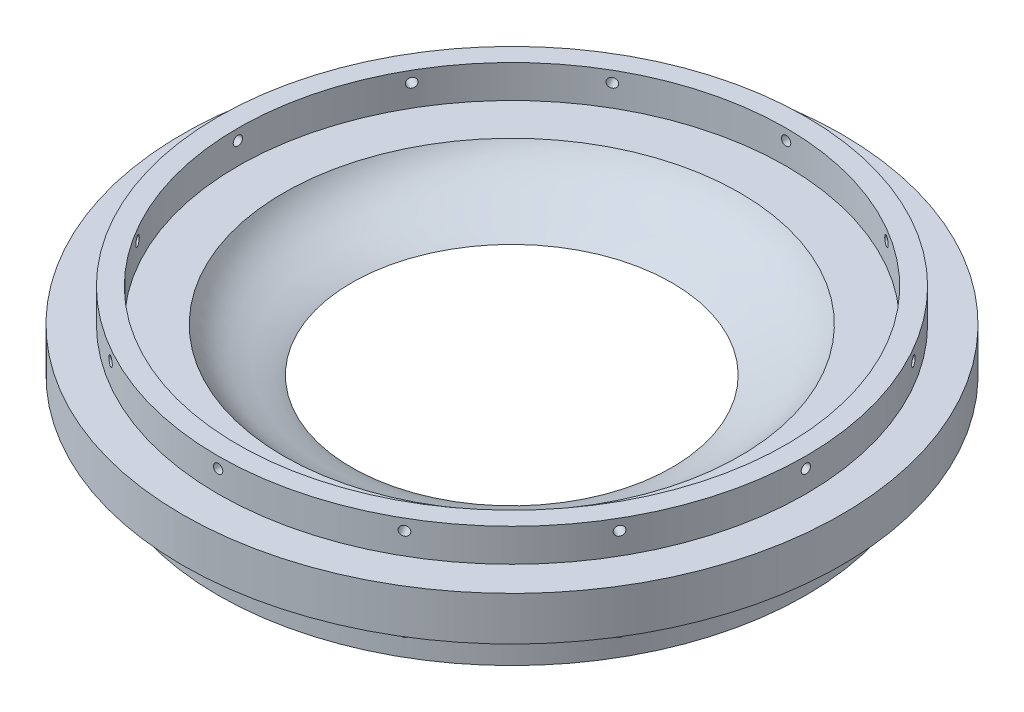
SolidWorks part; units mm, degrees
material "6061-T6 (SS)"
ref_plane "Front Plane" through (0, 0, 0) normal (0, 0, 1) x (1, 0, 0)
ref_plane "Top Plane" through (0, 0, 0) normal (0, 1, 0) x (1, 0, 0)
ref_plane "Right Plane" through (0, 0, 0) normal (1, 0, 0) x (0, 0, -1)
sketch "Sketch1" plane through (0, 0, 0) normal (0, 1, 0) x (1, 0, 0)
  line L5 (0, 0) -> (127.635, 0)
  line L6 (0, 0) -> (0, 127.635)
  line L7 (0, 127.635) -> (127.635, 127.635)
  line L8 (127.635, 0) -> (127.635, 127.635)
  dimension "D1" = 127.635
  dimension "D2" = 127.635
extrude "Boss-Extrude1" add sketch "Sketch1" along normal blind 12.7 contours L5 L8 L7 L6
sketch "Sketch12" plane through (0, 0, 0) normal (0, -1, 0) x (1, 0, 0)
  line L0 (63.8175, 0) -> (63.8175, -127.635) construction
  line L1 (0, 0) -> (127.635, 0) construction
  line L2 (0, -127.635) -> (127.635, -127.635) construction
  line L3 (0, -63.8175) -> (127.635, -63.8175) construction
  line L4 (0, 0) -> (0, -127.635) construction
  line L5 (127.635, 0) -> (127.635, -127.635) construction
  circle A0 centre (63.8175, -63.8175) radius 95.4151
  dimension "D1" = 190.8302
extrude "Boss-Extrude2" add sketch "Sketch12" against normal up to surface (12.7 mm away) contours A0 up to face at (63.8175, 12.7, -63.8175)
sketch "Sketch5" plane through (0, 12.7, 0) normal (0, 1, 0) x (1, 0, 0)
  circle A0 centre (63.8175, 63.8175) radius 46.355
  circle A3 centre (63.8175, 63.8175) radius 95.4151 construction
  dimension "D1" = 92.71
extrude "Cut-Extrude1" cut sketch "Sketch5" against normal blind 9.525
sketch "Sketch14" plane through (0, 12.7, 0) normal (0, -1, 0) x (1, 0, 0)
  line L0 (63.8175, -63.8175) -> (147.6375, -63.8175) construction
  line L1 (0, -19.2087) -> (0, 19.2087) construction
  line L2 (147.6375, -63.8175) -> (152.7175, -63.8175)
  line L3 (136.3808, -105.7742) -> (140.8401, -108.2104)
  circle A0 centre (63.8175, -63.8175) radius 46.355 construction
  arc A2 (147.6375, -63.8175) -> (136.3808, -105.7742) centre (63.8175, -63.8175) cw
  arc A3 (152.7175, -63.8175) -> (140.8401, -108.2104) centre (63.8175, -63.8175) cw
  point P0 (63.8175, -63.8175)
  dimension "D1" = 83.82
  dimension "D2" = 88.9
  dimension "D3" = 46.482
  dimension "D4" = 43.942
ref_plane "Support mirror reference plane" through (0, 4.7625, 0) normal (0, 1, 0) x (1, 0, 0)
sketch "Sketch25" plane through (0, 12.7, 0) normal (0, -1, 0) x (1, 0, 0)
  line L0 (63.8175, -63.8175) -> (123.0872, -4.5478) construction
  line L2 (123.0872, -4.5478) -> (126.6793, -0.9557)
  line L3 (144.7953, -42.1754) -> (149.6712, -40.7448)
  line L5 (63.8175, -63.8175) -> (147.6375, -63.8175) construction
  arc A2 (123.0872, -4.5478) -> (144.7953, -42.1754) centre (63.8175, -63.8175) cw
  arc A3 (126.6793, -0.9557) -> (149.6712, -40.7448) centre (63.8175, -63.8175) cw
  point P0 (63.8175, -63.8175)
  dimension "D1" = 83.82
  dimension "D2" = 88.9
  dimension "D3" = 46.482
  dimension "D4" = 43.942
  dimension "D5" = 45
sketch "Sketch30" plane through (0, 0, 0) normal (0, -1, 0) x (1, 0, 0)
  circle A0 centre (63.8175, -63.8175) radius 85.09
  circle A1 centre (63.8175, -63.8175) radius 79.375
  dimension "D1" = 170.18
  dimension "D2" = 158.75
extrude "Boss-Extrude3" add sketch "Sketch30" along normal blind 12.7
mirror "Mirror1" about plane through (0, 4.7625, 0) normal (0, 1, 0) of "Boss-Extrude3"
sketch "Sketch31" plane through (0, 0, 0) normal (0, -1, 0) x (-1, 0, 0)
  line L0 (-63.8175, -52.481) -> (-63.8175, 177.7216) construction
ref_plane "Plane1" through (0, 0, -148.9075) normal (0, 0, -1) x (-1, 0, 0)
ref_plane "Plane2" through (63.8175, 0, 0) normal (-1, 0, 0) x (0, 0, -1)
sketch "Sketch32" plane through (0, 0, -148.9075) normal (0, 0, -1) x (-1, 0, 0)
  line L4 (-63.8175, -87.3125) -> (-63.8175, 87.3125) construction
  line L5 (-148.9075, 0) -> (21.2725, 0) construction
  line L6 (21.2725, 12.7) -> (-148.9075, 12.7) construction
  circle A0 centre (-63.8175, -6.35) radius 1.3526
  circle A1 centre (-63.8175, 19.05) radius 1.3525
  dimension "D1" = 2.7051
  dimension "D2" = 2.7051
  dimension "D3" = 6.35
  dimension "D4" = 6.35
extrude "Cut-Extrude4" cut sketch "Sketch32" against normal blind 15.24
pattern_circular "CirPattern2" count 12 over 360 about axis through (63.8175, -12.7, -63.8175) along (0, 1, 0) of "Cut-Extrude4"
ref_plane "Plane3" through (0, 0, -63.754) normal (0, 0, 1) x (1, 0, 0)
sketch "Sketch35" plane through (0, 0, -63.754) normal (0, 0, 1) x (1, 0, 0)
  line L3 (110.1725, 12.7) -> (17.4625, 12.7) construction
  line L4 (63.8175, 12.7) -> (129.8575, 12.7)
  line L6 (63.8175, -10.3302) -> (63.8175, 21.6129) construction
  line L8 (110.1725, 0) -> (63.8175, 0)
  line L9 (63.8175, 0) -> (63.8175, 12.7)
  circle A0 centre (63.8175, 19.05) radius 1.3526 construction
  circle A1 centre (63.8175, 19.05) radius 1.3525
  spline S0 degree 3 poles (129.8575, 12.7) (125.5567, 5.3002) (116.9453, 3.9994) (110.1725, 0) knots 0 0 0 0 1 1 1 1
  dimension "D1" = 12.7
  dimension "D2" = 46.355
  dimension "D3" = 66.04
revolve "Cut-Revolve1" cut sketch "Sketch35" angle 360 about L6
